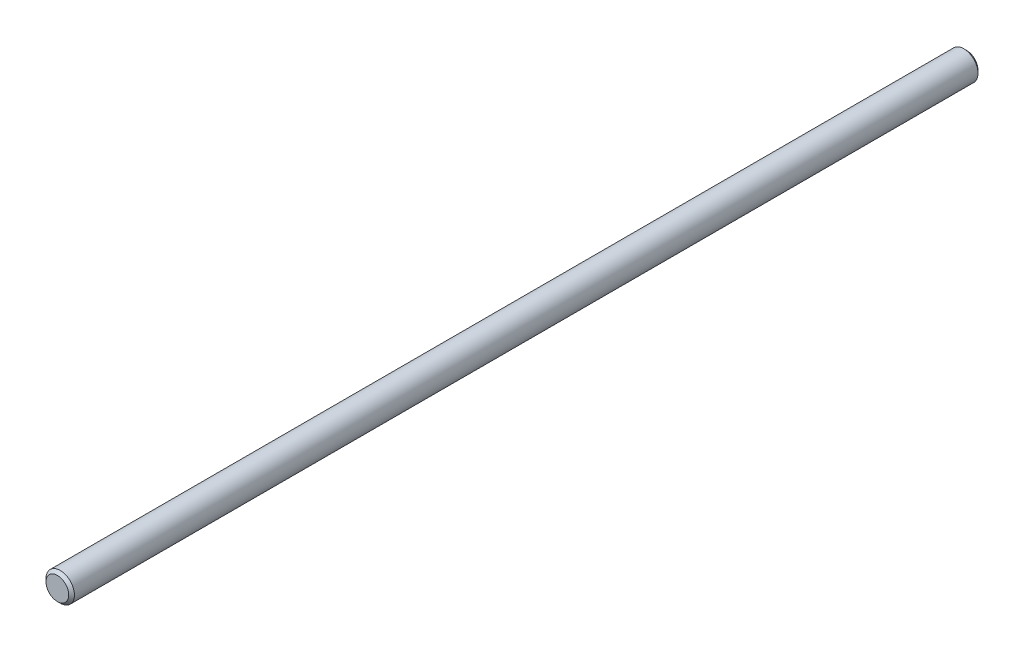
SolidWorks part; units mm, degrees
ref_plane "Front" through (0, 0, 0) normal (0, 0, 1) x (1, 0, 0)
ref_plane "Top" through (0, 0, 0) normal (0, 1, 0) x (1, 0, 0)
ref_plane "Right" through (0, 0, 0) normal (1, 0, 0) x (0, 0, -1)
sketch "Sketch1" plane through (0, 0, 0) normal (0, 0, 1) x (1, 0, 0)
  circle A0 centre (0, 0) radius 4.7625
  dimension "Diameter" = 9.525
sketch "Sketch2" plane through (0, 0, 0) normal (1, 0, 0) x (0, 0, -1)
  line L0 (-152.4, 0) -> (152.4, 0) construction
  line L1 (-101.6, 4.7625) -> (-101.6, -4.7625) construction
  line L2 (17.4625, 0) -> (-17.4625, 0) construction
  line L3 (101.6, 4.7625) -> (101.6, -4.7625) construction
  line L4 (-152.4, 4.7625) -> (-152.4, -4.7625) construction
  line L5 (152.4, 4.7625) -> (152.4, -4.7625) construction
  point P3 (-101.6, 0)
  point P8 (0, 0)
  point P9 (101.6, 0)
  point P15 (-152.4, 0)
  point P18 (152.4, 0)
  dimension "D1" = 9.525
  dimension "Length" = 304.8
  dimension "D2" = 50.8
  dimension "D3" = 50.8
sketch "Sketch3" plane through (0, 0, 0) normal (0, 0, 1) x (1, 0, 0)
  circle A0 centre (0, 0) radius 4.7625
  dimension "D1" = 9.525
extrude "Boss-Extrude1" add sketch "Sketch3" along normal mid plane 304.8
chamfer "Chamfer1" distance 0.9525 angle 45 2 edges at (4.7625, 0, -152.4) (4.7625, 0, 152.4)
equation "\"D1@Sketch3\" = \"Diameter@Sketch1\""
equation "\"D1@Boss-Extrude1\"=\"Length@Sketch2\""
equation "\"D1@Chamfer1\" = \"Diameter@Sketch1\" * .1"
equation "\"D1@Sketch2\" = \"Diameter@Sketch1\""
